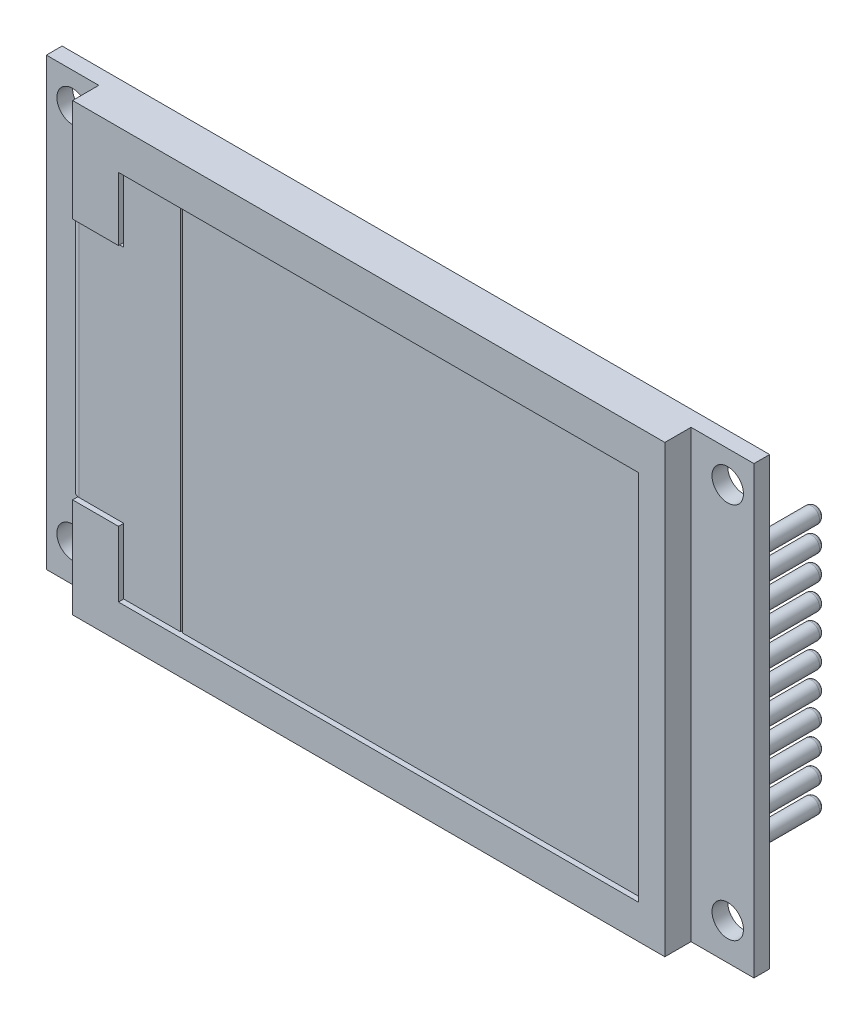
SolidWorks part; units mm, degrees
ref_plane "Ebene vorne" through (0, 0, 0) normal (0, 0, 1) x (1, 0, 0)
ref_plane "Ebene oben" through (0, 0, 0) normal (0, 1, 0) x (1, 0, 0)
ref_plane "Ebene rechts" through (0, 0, 0) normal (1, 0, 0) x (0, 0, -1)
sketch "Skizze1" plane through (0, 0, 0) normal (0, 0, 1) x (1, 0, 0)
  line L1 (-33.75, -21.25) -> (33.75, -21.25)
  line L2 (-33.75, -21.25) -> (-33.75, 21.25)
  line L3 (-33.75, 21.25) -> (33.75, 21.25)
  line L4 (33.75, -21.25) -> (33.75, 21.25)
  line L5 (-33.75, -21.25) -> (33.75, 21.25) construction
  line L6 (-33.75, 21.25) -> (33.75, -21.25) construction
  point P0 (0, 0)
  dimension "D1" = 67.5
  dimension "D2" = 42.5
extrude "Aufsatz-Linear austragen1" add sketch "Skizze1" along normal blind 1.5
sketch "Skizze2" plane through (0, 0, 1.5) normal (0, 0, 1) x (1, 0, 0)
  line L0 (-33.75, -21.25) -> (33.75, -21.25) construction
  line L1 (27.75, 21.25) -> (-28.75, 21.25)
  line L2 (27.75, 21.25) -> (27.75, -21.25)
  line L3 (27.75, -21.25) -> (-28.75, -21.25)
  line L4 (-28.75, 21.25) -> (-28.75, -21.25)
  line L5 (33.75, 21.25) -> (-33.75, 21.25) construction
  line L7 (-33.75, 21.25) -> (-33.75, -21.25) construction
  line L8 (33.75, -21.25) -> (33.75, 21.25) construction
  point P0 (0, 0)
  dimension "D1" = 5
  dimension "D2" = 6
  dimension "D3" = 0
extrude "Aufsatz-Linear austragen2" add sketch "Skizze2" along normal blind 2.5 separate body
sketch "Skizze3" plane through (0, 0, 1.5) normal (0, 0, 1) x (1, 0, 0)
  line L0 (-33.75, -21.25) -> (33.75, -21.25) construction
  line L1 (-33.75, 21.25) -> (-33.75, -21.25) construction
  circle A0 centre (-31.25, -17.75) radius 1.5
  circle A1 centre (-31.25, 18.25) radius 1.5
  dimension "D1" = 3
  dimension "D2" = 3.5
  dimension "D3" = 2.5
  dimension "D4" = 2
extrude "Schnitt-Linear austragen1" cut sketch "Skizze3" against normal through all
pattern_linear "Lineares Muster1" count 2 spacing 62.5 along (1, 0, 0) of "Schnitt-Linear austragen1"
sketch "Skizze4" plane through (0, 0, 0) normal (0, 0, -1) x (-1, 0, 0)
  line L0 (18.75, -21.25) -> (18.75, -11.25)
  line L1 (33.75, -21.25) -> (-33.75, -21.25) construction
  line L2 (18.75, -11.25) -> (15.75, -9.25)
  line L3 (15.75, -9.25) -> (15.75, -4.25)
  line L4 (15.75, -4.25) -> (-7.25, -4.25)
  line L5 (-7.25, -4.25) -> (-7.25, -21.25)
  line L6 (-7.25, -21.25) -> (18.75, -21.25)
  line L7 (33.75, 21.25) -> (33.75, -21.25) construction
  dimension "D1" = 15
  dimension "D2" = 10
  dimension "D3" = 17
  dimension "D4" = 26
  dimension "D5" = 3
  dimension "D6" = 5
extrude "Aufsatz-Linear austragen3" add sketch "Skizze4" along normal blind 3 separate body
sketch "Skizze5" plane through (0, 0, 4) normal (0, 0, 1) x (1, 0, 0)
  line L0 (-28.75, 21.25) -> (-28.75, -21.25) construction
  line L1 (25.25, -18) -> (-18.75, -18)
  line L2 (25.25, -18) -> (25.25, 17.5)
  line L3 (25.25, 17.5) -> (-18.75, 17.5)
  line L4 (-18.75, -18) -> (-18.75, 17.5)
  dimension "D1" = 35.5
  dimension "D2" = 44
  dimension "D3" = 17.5
  dimension "D4" = 10
extrude "Schnitt-Linear austragen2" cut sketch "Skizze5" against normal blind 0.5
sketch "Skizze6" plane through (0, 0, 4) normal (0, 0, 1) x (1, 0, 0)
  line L0 (-18.75, 17.5) -> (-24.3753, 17.5)
  line L1 (-24.3753, 17.5) -> (-24.3753, 11.4512)
  line L2 (-24.3753, 11.4512) -> (-28.75, 11.4512)
  line L3 (-28.75, 21.25) -> (-28.75, -21.25) construction
  line L4 (-28.75, 11.4512) -> (-28.75, -11.745)
  line L5 (-28.75, -11.745) -> (-24.3753, -11.745)
  line L6 (-24.3753, -11.745) -> (-24.3753, -18)
  line L7 (-24.3753, -18) -> (-18.75, -18)
  line L8 (-18.75, -18) -> (-18.75, 17.5)
  dimension "D1" = 0
extrude "Schnitt-Linear austragen3" cut sketch "Skizze6" against normal blind 0.9
sketch "Skizze7" plane through (0, 0, 3.1) normal (0, 0, 1) x (1, 0, 0)
  line L0 (-18.75, 17.3) -> (-24.1753, 17.3)
  line L1 (-18.75, -18) -> (-18.75, 17.5) construction
  line L2 (-24.1753, 17.3) -> (-24.1753, 11.2512)
  line L3 (-24.1753, 11.2512) -> (-29.25, 11.2512)
  line L4 (-29.25, 11.2512) -> (-29.25, -11.545)
  line L5 (-29.25, -11.545) -> (-24.1753, -11.545)
  line L6 (-24.1753, -11.545) -> (-24.1753, -17.8)
  line L7 (-24.1753, -17.8) -> (-18.75, -17.8)
  line L8 (-18.75, -17.8) -> (-18.75, 17.3)
  line L9 (-18.75, 17.5) -> (-24.3753, 17.5) construction
  line L10 (-24.3753, 17.5) -> (-24.3753, 11.4512) construction
  line L11 (-24.3753, 11.4512) -> (-28.75, 11.4512) construction
  line L12 (-28.75, -11.745) -> (-24.3753, -11.745) construction
  line L13 (-24.3753, -11.745) -> (-24.3753, -18) construction
  line L14 (-24.3753, -18) -> (-18.75, -18) construction
  line L15 (-28.75, 11.4512) -> (-28.75, -11.745) construction
  point P20 (-21.5627, -18)
  dimension "D1" = 0.2
  dimension "D2" = 0.2
  dimension "D3" = 0.2
  dimension "D4" = 0.2
  dimension "D5" = 0.2
  dimension "D6" = 0.2
  dimension "D7" = 0.5
extrude "Aufsatz-Linear austragen4" add sketch "Skizze7" against normal up to surface (1.6 mm away) and the other way blind 0.6 up to face at (32.75, 18.25, 1.5)
fillet "Verrundung6" radius 0.8 1 edges at (-29.25, -0.1469, 3.7)
sketch "Skizze8" plane through (0, -21.25, 0) normal (0, -1, 0) x (1, 0, 0)
  line L0 (7.25, -3) -> (-18.75, -3) construction
  line L1 (6.75, -0.5) -> (-18.25, -0.5)
  line L2 (6.75, -0.5) -> (6.75, -2.5)
  line L3 (6.75, -2.5) -> (-18.25, -2.5)
  line L4 (-18.25, -0.5) -> (-18.25, -2.5)
  line L5 (-33.75, 0) -> (33.75, 0) construction
  line L6 (7.25, -3) -> (7.25, 0) construction
  line L7 (-18.75, -3) -> (-18.75, 0) construction
  dimension "D1" = 0.5
  dimension "D2" = 0.5
  dimension "D3" = 0.5
  dimension "D4" = 0.5
extrude "Schnitt-Linear austragen4" cut sketch "Skizze8" against normal blind 9.56
sketch "Skizze9" plane through (0, 0, 0) normal (0, 0, -1) x (-1, 0, 0)
  line L0 (33.75, -21.25) -> (-33.75, -21.25) construction
  line L1 (-32.75, -13.75) -> (-29.75, -13.75)
  line L2 (-32.75, -13.75) -> (-32.75, 13.75)
  line L3 (-32.75, 13.75) -> (-29.75, 13.75)
  line L4 (-29.75, -13.75) -> (-29.75, 13.75)
  line L5 (-33.75, 21.25) -> (33.75, 21.25) construction
  line L6 (-33.75, -21.25) -> (-33.75, 21.25) construction
  dimension "D1" = 7.5
  dimension "D2" = 7.5
  dimension "D3" = 3
  dimension "D4" = 1
extrude "Aufsatz-Linear austragen5" add sketch "Skizze9" along normal blind 1
sketch "Skizze10" plane through (0, 0, -1) normal (0, 0, -1) x (-1, 0, 0)
  line L0 (-32.75, 13.75) -> (-32.75, -13.75) construction
  line L1 (-32.75, -13.75) -> (-29.75, -13.75) construction
  circle A0 centre (-31.25, -12.25) radius 0.75
  circle A1 centre (-31.25, -9.85) radius 0.75
  circle A2 centre (-31.25, -7.45) radius 0.75
  circle A3 centre (-31.25, -5.05) radius 0.75
  circle A4 centre (-31.25, -2.65) radius 0.75
  circle A5 centre (-31.25, -0.25) radius 0.75
  circle A6 centre (-31.25, 2.15) radius 0.75
  circle A7 centre (-31.25, 4.55) radius 0.75
  circle A8 centre (-31.25, 6.95) radius 0.75
  circle A9 centre (-31.25, 9.35) radius 0.75
  circle A10 centre (-31.25, 11.75) radius 0.75
  dimension "D1" = 1.5
  dimension "D2" = 1.5
  dimension "D3" = 1.5
  dimension "D4" = 11
extrude "Aufsatz-Linear austragen6" add sketch "Skizze10" along normal blind 6
fillet "Verrundung18" radius 0.5 11 edges at (30.5, -0.25, -7) (30.5, -2.65, -7) (30.5, -5.05, -7) (30.5, -7.45, -7) (30.5, -9.85, -7) (30.5, -12.25, -7) (30.5, 2.15, -7) (30.5, 4.55, -7) (30.5, 6.95, -7) (30.5, 9.35, -7) (30.5, 11.75, -7)
